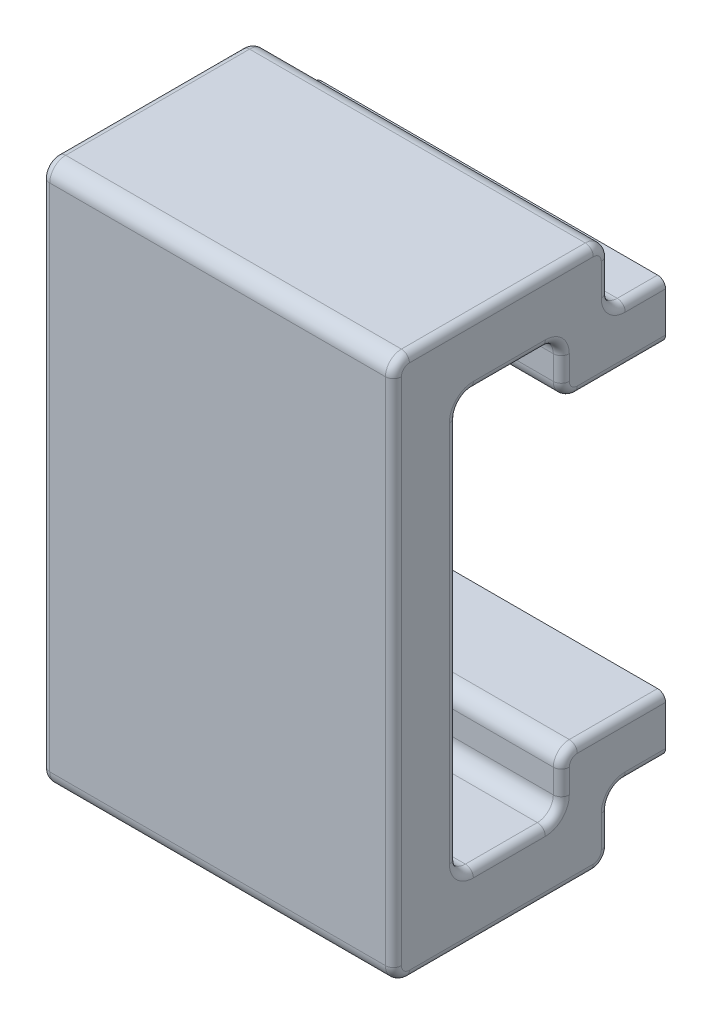
SolidWorks part; units mm, degrees
ref_plane "Front Plane" through (0, 0, 0) normal (0, 0, 1) x (1, 0, 0)
ref_plane "Top Plane" through (0, 0, 0) normal (0, 1, 0) x (1, 0, 0)
ref_plane "Right Plane" through (0, 0, 0) normal (1, 0, 0) x (0, 0, -1)
sketch "Sketch1" plane through (0, 0, 0) normal (1, 0, 0) x (0, 0, -1)
  line L0 (0, 0) -> (37.4171, 0) construction
  line L3 (2.0848, 11.95) -> (2.0848, -11.95)
  line L4 (0, -16.95) -> (-0.9152, -16.95)
  line L5 (-1.9152, -15.95) -> (-1.9152, 15.95)
  line L6 (-0.9152, 16.95) -> (0, 16.95)
  line L7 (0, 16.95) -> (10.5848, 16.95)
  line L8 (11.5848, 15.95) -> (11.5848, 13.95)
  line L9 (12.5848, 12.95) -> (15.1071, 12.95)
  line L13 (15.1071, 9.45) -> (9.5848, 9.45)
  line L14 (8.5848, 10.45) -> (8.5848, 11.95)
  line L15 (7.5848, 12.95) -> (3.0848, 12.95)
  line L16 (7.5848, -12.95) -> (3.0848, -12.95)
  line L17 (8.5848, -10.45) -> (8.5848, -11.95)
  line L18 (15.1071, -9.45) -> (9.5848, -9.45)
  line L22 (12.5848, -12.95) -> (15.1071, -12.95)
  line L23 (11.5848, -15.95) -> (11.5848, -13.95)
  line L24 (0, -16.95) -> (10.5848, -16.95)
  line L26 (15.1071, -12.95) -> (15.1071, -9.45)
  line L27 (15.1071, 12.95) -> (15.1071, 9.45)
  arc A5 (7.5848, -12.95) -> (8.5848, -11.95) centre (7.5848, -11.95) ccw
  arc A6 (8.5848, -10.45) -> (9.5848, -9.45) centre (9.5848, -10.45) cw
  arc A7 (12.5848, -12.95) -> (11.5848, -13.95) centre (12.5848, -13.95) ccw
  arc A12 (11.5848, -15.95) -> (10.5848, -16.95) centre (10.5848, -15.95) cw
  arc A13 (-0.9152, -16.95) -> (-1.9152, -15.95) centre (-0.9152, -15.95) cw
  arc A14 (3.0848, -12.95) -> (2.0848, -11.95) centre (3.0848, -11.95) cw
  arc A15 (-1.9152, 15.95) -> (-0.9152, 16.95) centre (-0.9152, 15.95) cw
  arc A16 (3.0848, 12.95) -> (2.0848, 11.95) centre (3.0848, 11.95) ccw
  arc A17 (8.5848, 11.95) -> (7.5848, 12.95) centre (7.5848, 11.95) ccw
  arc A18 (9.5848, 9.45) -> (8.5848, 10.45) centre (9.5848, 10.45) cw
  arc A23 (11.5848, 13.95) -> (12.5848, 12.95) centre (12.5848, 13.95) ccw
  arc A24 (10.5848, 16.95) -> (11.5848, 15.95) centre (10.5848, 15.95) cw
  point P6 (15.1071, -12.95)
  point P7 (0, 0)
  point P15 (15.1071, -9.45)
  point P16 (15.0972, -12.95)
  point P21 (8.5848, -12.95)
  point P26 (8.5848, -9.45)
  point P29 (11.5848, -12.95)
  point P32 (16.0848, -12.95)
  point P33 (15.1071, 9.45)
  point P34 (15.1107, -9.2672)
  point P37 (19.0848, -9.45)
  point P42 (19.0848, -15.95)
  point P43 (15.1071, 12.95)
  point P44 (15.1071, -9.45)
  point P45 (16.0848, -15.95)
  point P48 (11.5848, -16.95)
  point P53 (2.0848, -12.95)
  point P58 (2.0848, 12.95)
  point P61 (8.5848, 12.95)
  point P64 (8.5848, 9.45)
  point P67 (19.0848, 9.45)
  point P70 (19.0848, 15.95)
  point P73 (16.0848, 15.95)
  point P76 (16.0848, 12.95)
  point P79 (11.5848, 12.95)
  point P82 (11.5848, 16.95)
  dimension "D1" = 4
  dimension "D2" = 3
  dimension "D6" = 4
  dimension "D8" = 1
  dimension "D3" = 3.5
  dimension "D7" = 3
  dimension "D10" = 25.9
extrude "Boss-Extrude1" add sketch "Sketch1" along normal blind 22
fillet "Fillet1" radius 0.5 26 edges at (22, -9.45, -12.346) (22, -12.95, -13.846) (22, -13.2429, -11.8777) (22, -11.2, -8.5848) (22, -9.7429, -8.8777) (22, -12.6571, -8.292) (22, -14.95, -11.5848) (22, -16.6571, -11.292) (22, -16.95, -4.8348) (22, -16.6571, 1.6223) (22, -12.6571, -2.3777) (22, -12.95, -5.3348) (22, 0, -2.0848) (22, 12.6571, -2.3777) (22, 0, 1.9152) (22, 16.6571, 1.6223) (22, 12.95, -5.3348) (22, 12.6571, -8.292) (22, 11.2, -8.5848) (22, 9.7429, -8.8777) (22, 9.45, -12.346) (22, 12.95, -13.846) (22, 13.2429, -11.8777) (22, 14.95, -11.5848) (22, 16.6571, -11.292) (22, 16.95, -4.8348)
fillet "Fillet2" radius 0.5 26 edges at (0, -12.95, -13.846) (0, -9.45, -12.346) (0, -9.7429, -8.8777) (0, -11.2, -8.5848) (0, -13.2429, -11.8777) (0, -14.95, -11.5848) (0, -16.6571, -11.292) (0, -12.6571, -8.292) (0, -12.95, -5.3348) (0, -12.6571, -2.3777) (0, -16.95, -4.8348) (0, -16.6571, 1.6223) (0, 0, 1.9152) (0, 0, -2.0848) (0, 16.6571, 1.6223) (0, 12.6571, -2.3777) (0, 12.95, -5.3348) (0, 16.95, -4.8348) (0, 16.6571, -11.292) (0, 14.95, -11.5848) (0, 11.2, -8.5848) (0, 12.6571, -8.292) (0, 9.7429, -8.8777) (0, 13.2429, -11.8777) (0, 12.95, -13.846) (0, 9.45, -12.346)
ref_plane "Plane1" through (0, 0, -15.1071) normal (0, 0, -1) x (-1, 0, 0)
sketch "Sketch11" plane through (0, 0, -15.1071) normal (0, 0, -1) x (-1, 0, 0)
  line L1 (-20, 11.85) -> (-2, 11.85)
  line L2 (-20, 11.85) -> (-20, 10.55)
  line L3 (-20, 10.55) -> (-2, 10.55)
  line L4 (-2, 11.85) -> (-2, 10.55)
  line L7 (-20, -10.55) -> (-2, -10.55)
  line L8 (-20, -10.55) -> (-20, -11.85)
  line L9 (-20, -11.85) -> (-2, -11.85)
  line L10 (-2, -10.55) -> (-2, -11.85)
  line L20 (-21.5, 12.95) -> (-0.5, 12.95) construction
  line L24 (-22, 9.95) -> (-22, 12.45) construction
  line L25 (0, 9.95) -> (0, 12.45) construction
  line L26 (-21.5, 9.45) -> (-0.5, 9.45) construction
  line L27 (-22, -12.45) -> (-22, -9.95) construction
  line L28 (0, -12.45) -> (0, -9.95) construction
  line L29 (-21.5, -9.45) -> (-0.5, -9.45) construction
  line L30 (-21.5, -12.95) -> (-0.5, -12.95) construction
  dimension "D1" = 1.1
  dimension "D2" = 1.1
  dimension "D3" = 1.1
  dimension "D4" = 1.1
  dimension "D5" = 2
  dimension "D6" = 2
  dimension "D7" = 2
  dimension "D8" = 2
extrude "Cut-Extrude1" cut sketch "Sketch11" against normal blind 2.1
